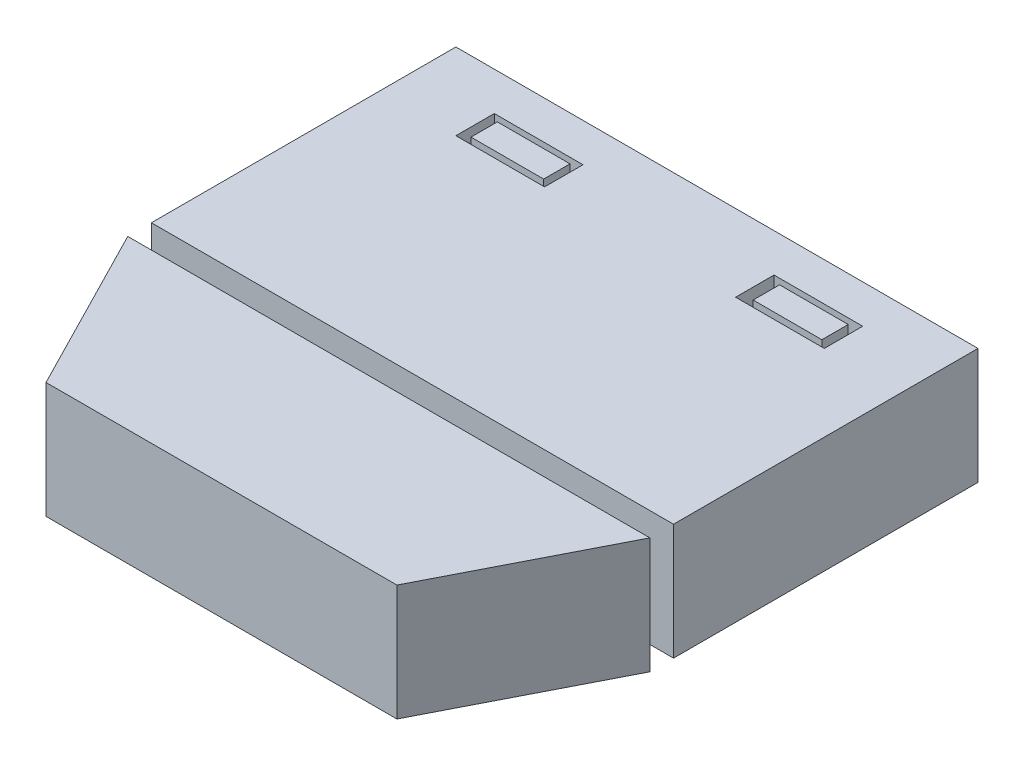
SolidWorks part; units mm, degrees
ref_plane "Front Plane" through (0, 0, 0) normal (0, 0, 1) x (1, 0, 0)
ref_plane "Top Plane" through (0, 0, 0) normal (0, 1, 0) x (1, 0, 0)
ref_plane "Right Plane" through (0, 0, 0) normal (1, 0, 0) x (0, 0, -1)
sketch "Sketch1" plane through (0, 0, 0) normal (0, 1, 0) x (1, 0, 0)
  line L0 (0, 13.758) -> (45, 13.758)
  line L3 (0, 40) -> (45, 40)
  line L9 (45, 11.7197) -> (0, 11.7197)
  line L12 (22.5, 13.758) -> (22.5, 11.7197) construction
  line L13 (6.6242, 36.6879) -> (14.2675, 36.6879)
  line L14 (6.6242, 36.6879) -> (6.6242, 33.3758)
  line L15 (6.6242, 33.3758) -> (14.2675, 33.3758)
  line L16 (14.2675, 36.6879) -> (14.2675, 33.3758)
  line L17 (38.3758, 33.3758) -> (30.7325, 33.3758)
  line L18 (30.7325, 36.6879) -> (30.7325, 33.3758)
  line L19 (38.3758, 36.6879) -> (30.7325, 36.6879)
  line L20 (38.3758, 36.6879) -> (38.3758, 33.3758)
  line L21 (0, 13.758) -> (0, 40)
  line L23 (0, 40) -> (45, 40)
  line L24 (45, 13.758) -> (45, 40)
  line L25 (45, 13.758) -> (45, 40)
  line L26 (0, 11.7197) -> (7.3776, -2.7039)
  line L27 (45, 11.7197) -> (37.6224, -2.7039)
  line L28 (7.3776, -2.7039) -> (22.5, -2.7039)
  line L29 (22.5, -2.7039) -> (37.6224, -2.7039)
  line L31 (7.3776, 36.1945) -> (13.6416, 36.1945)
  line L32 (7.3776, 36.1945) -> (7.3776, 33.9231)
  line L33 (7.3776, 33.9231) -> (13.6416, 33.9231)
  line L34 (13.6416, 36.1945) -> (13.6416, 33.9231)
  line L35 (31.6991, 36.1945) -> (37.6224, 36.1945)
  line L36 (31.6991, 36.1945) -> (31.6991, 33.9231)
  line L37 (31.6991, 33.9231) -> (37.6224, 33.9231)
  line L38 (37.6224, 36.1945) -> (37.6224, 33.9231)
  dimension "D2" = 45
extrude "Boss-Extrude3" add sketch "Sketch1" along normal blind 10 contours L28 L29 L27 L9 L26 | L0 L24 L3 L21 L19 L20 L17 L18 L13 L16 L15 L14 | L34 L31 L32 L33 | L38 L35 L36 L37
